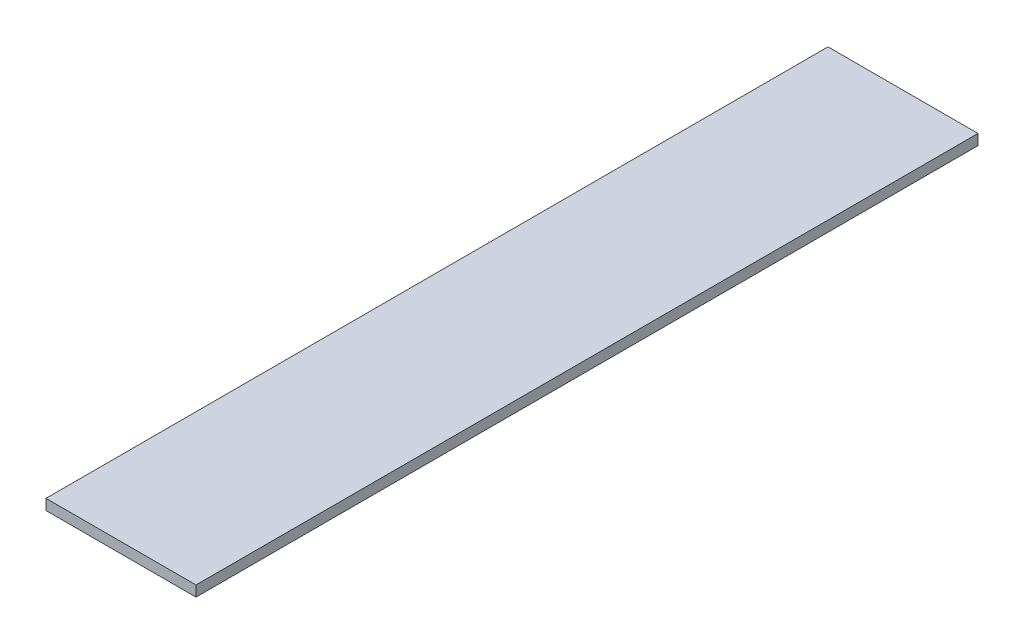
SolidWorks part; units mm, degrees
material "6061-O (SS)"
ref_plane "Front Plane" through (0, 0, 0) normal (0, 0, 1) x (1, 0, 0)
ref_plane "Top Plane" through (0, 0, 0) normal (0, 1, 0) x (1, 0, 0)
ref_plane "Right Plane" through (0, 0, 0) normal (1, 0, 0) x (0, 0, -1)
sketch "Sketch1" plane through (0, 0, 0) normal (0, 1, 0) x (1, 0, 0)
  line L1 (0, 0) -> (90, 0)
  line L2 (0, 0) -> (0, 469.2)
  line L3 (0, 469.2) -> (90, 469.2)
  line L4 (90, 0) -> (90, 469.2)
  dimension "D1" = 469.2
  dimension "D2" = 90
extrude "Boss-Extrude1" add sketch "Sketch1" along normal blind 6.35
